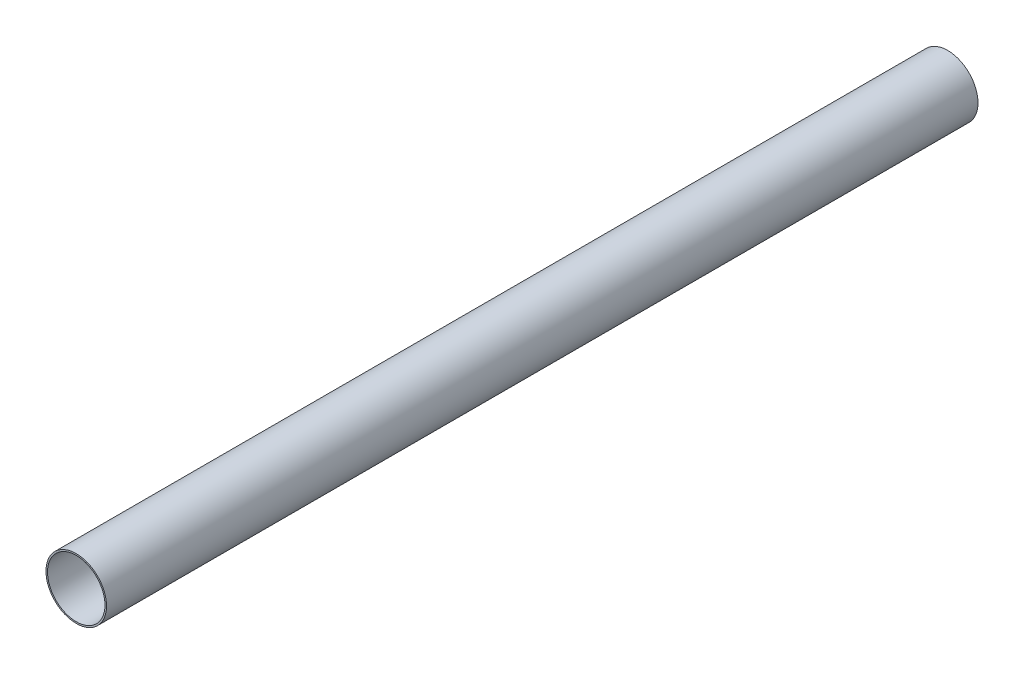
SolidWorks part; units mm, degrees
material "S-Glass Fiber"
ref_plane "Front Plane" through (0, 0, 0) normal (0, 0, 1) x (1, 0, 0)
ref_plane "Top Plane" through (0, 0, 0) normal (0, 1, 0) x (1, 0, 0)
ref_plane "Right Plane" through (0, 0, 0) normal (1, 0, 0) x (0, 0, -1)
sketch "Sketch1" plane through (0, 0, 0) normal (0, 0, 1) x (1, 0, 0)
  circle A0 centre (0, 0) radius 49.403
  circle A1 centre (0, 0) radius 52.07
  dimension "D1" = 98.806
  dimension "D2" = 104.14
extrude "Boss-Extrude1" add sketch "Sketch1" along normal blind 1498.6
sketch "Sketch2" plane through (0, 0, 0) normal (1, 0, 0) x (0, 0, -1)
  line L0 (-1498.6, 0) -> (0, 0) construction
  line L1 (-1498.6, 52.07) -> (-1498.6, -52.07) construction
